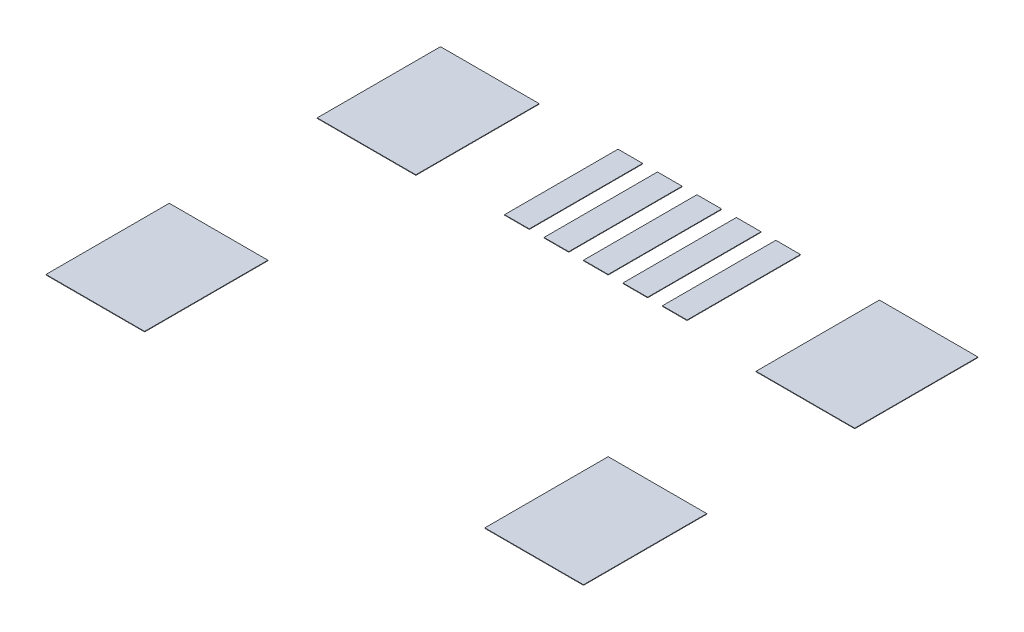
SolidWorks part; units mm, degrees
material "普通碳钢"
ref_plane "Front Plane" through (0, 0, 0) normal (0, 0, 1) x (1, 0, 0)
ref_plane "Top Plane" through (0, 0, 0) normal (0, 1, 0) x (1, 0, 0)
ref_plane "Right Plane" through (0, 0, 0) normal (1, 0, 0) x (0, 0, -1)
sketch "Sketch1" plane through (0, 0, 0) normal (0, 1, 0) x (1, 0, 0)
  line L0 (-4.45, 0) -> (-4.45, 2.5) construction
  line L1 (-5.45, 8) -> (-3.45, 8)
  line L2 (-5.45, 8) -> (-5.45, 5.5)
  line L3 (-5.45, 5.5) -> (-3.45, 5.5)
  line L4 (-3.45, 8) -> (-3.45, 5.5)
  line L5 (-5.45, 2.5) -> (-3.45, 2.5)
  line L6 (-5.45, 2.5) -> (-5.45, 0)
  line L7 (-5.45, 0) -> (-3.45, 0)
  line L8 (-3.45, 2.5) -> (-3.45, 0)
  line L9 (3.45, 8) -> (5.45, 8)
  line L10 (3.45, 8) -> (3.45, 5.5)
  line L11 (3.45, 5.5) -> (5.45, 5.5)
  line L12 (5.45, 8) -> (5.45, 5.5)
  line L13 (3.45, 2.5) -> (5.45, 2.5)
  line L14 (3.45, 2.5) -> (3.45, 0)
  line L15 (3.45, 0) -> (5.45, 0)
  line L16 (5.45, 2.5) -> (5.45, 0)
  line L17 (4.45, 0) -> (4.45, 2.5) construction
  line L18 (0, -55) -> (0, 55) construction
  line L19 (-55, 0) -> (55, 0) construction
  line L20 (-5.45, 1.25) -> (-3.45, 1.25) construction
  line L21 (3.45, 1.25) -> (5.45, 1.25) construction
  line L23 (-1.85, 8) -> (-1.35, 8)
  line L24 (-1.85, 8) -> (-1.85, 5.7)
  line L25 (-1.85, 5.7) -> (-1.35, 5.7)
  line L26 (-1.35, 8) -> (-1.35, 5.7)
  line L27 (-1.05, 8) -> (-0.55, 8)
  line L28 (-1.05, 8) -> (-1.05, 5.7)
  line L29 (-1.05, 5.7) -> (-0.55, 5.7)
  line L30 (-0.55, 8) -> (-0.55, 5.7)
  line L31 (-0.25, 8) -> (0.25, 8)
  line L32 (-0.25, 8) -> (-0.25, 5.7)
  line L33 (-0.25, 5.7) -> (0.25, 5.7)
  line L34 (0.25, 8) -> (0.25, 5.7)
  line L35 (0.55, 8) -> (1.05, 8)
  line L36 (0.55, 8) -> (0.55, 5.7)
  line L37 (0.55, 5.7) -> (1.05, 5.7)
  line L38 (1.05, 8) -> (1.05, 5.7)
  line L39 (1.35, 8) -> (1.85, 8)
  line L40 (1.35, 8) -> (1.35, 5.7)
  line L41 (1.35, 5.7) -> (1.85, 5.7)
  line L42 (1.85, 8) -> (1.85, 5.7)
  dimension "D1" = 2.5
  dimension "D2" = 2
  dimension "D3" = 8.9
  dimension "D4" = 4.45
  dimension "D5" = 5.5
  dimension "D6" = 5.7
  dimension "D7" = 2.3
  dimension "D8" = 0.5
  dimension "D9" = 0.25
  dimension "D10" = 0.8
  dimension "D11" = 0.8
  dimension "D12" = 0.8
  dimension "D13" = 0.8
extrude "Boss-Extrude1" add sketch "Sketch1" against normal blind 0.01
